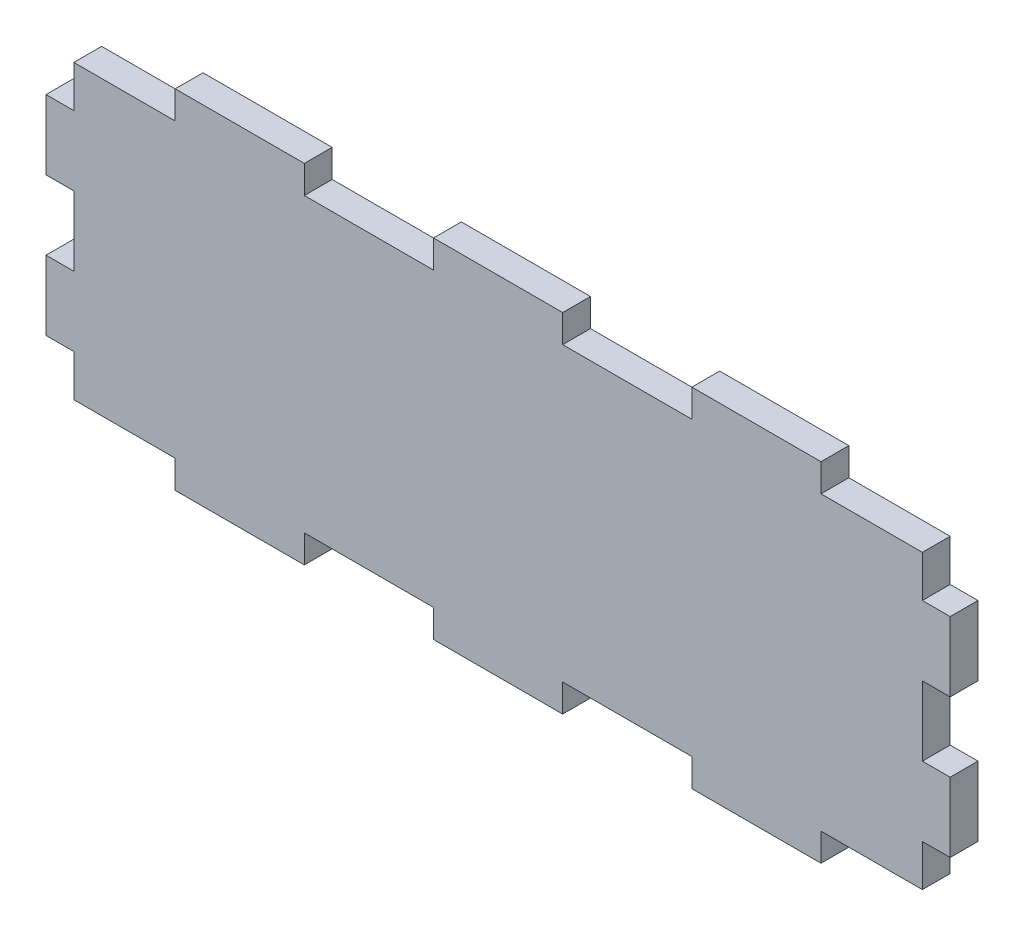
SolidWorks part; units mm, degrees
ref_plane "Front Plane" through (0, 0, 0) normal (0, 0, 1) x (1, 0, 0)
ref_plane "Top Plane" through (0, 0, 0) normal (0, 1, 0) x (1, 0, 0)
ref_plane "Right Plane" through (0, 0, 0) normal (1, 0, 0) x (0, 0, -1)
sketch "Buitenafmeting Rechthoek" plane through (0, 0, 0) normal (0, 0, 1) x (1, 0, 0)
  line L1 (0, 0) -> (130, 0)
  line L2 (0, 0) -> (0, 50)
  line L3 (0, 50) -> (130, 50)
  line L4 (130, 0) -> (130, 50)
  dimension "D1" = 130
  dimension "D2" = 50
extrude "Plaat" add sketch "Buitenafmeting Rechthoek" against normal blind 4
sketch "Tand Hor" plane through (0, 0, 0) normal (0, 0, 1) x (1, 0, 0)
  line L1 (130, 50) -> (0, 50) construction
  line L2 (0, 50) -> (18.5714, 50)
  line L3 (0, 50) -> (0, 46)
  line L4 (0, 46) -> (18.5714, 46)
  line L6 (18.5714, 50) -> (18.5714, 46)
  dimension "D1" = 4
  dimension "D2" = 18.5714
  dimension "D3" = 0
extrude "Tand Boven" cut sketch "Tand Hor" against normal through all
pattern_linear "Tanden Patroon Boven" count 4 spacing 37.1429 along (1, 0, 0) of "Tand Boven"
sketch "Tand Ver" plane through (0, 0, 0) normal (0, 0, 1) x (1, 0, 0)
  line L0 (0, 46) -> (0, 0) construction
  line L1 (0, 50) -> (4, 50)
  line L2 (0, 50) -> (0, 40)
  line L3 (0, 40) -> (4, 40)
  line L4 (4, 50) -> (4, 40)
  dimension "D1" = 4
  dimension "D2" = 10
  dimension "D3" = 50
extrude "Tand Links" cut sketch "Tand Ver" against normal through all
pattern_linear "Tanden Patroon Links" count 3 spacing 20 along (0, -1, 0) of "Tand Links"
sketch "Tand O" plane through (0, 0, 0) normal (0, 0, 1) x (1, 0, 0)
  line L0 (4, 0) -> (130, 0) construction
  line L1 (0, 0) -> (18.5714, 0)
  line L2 (0, 0) -> (0, 4)
  line L3 (0, 4) -> (18.5714, 4)
  line L4 (18.5714, 0) -> (18.5714, 4)
  dimension "D1" = 4
  dimension "D2" = 18.5714
  dimension "D3" = 0
extrude "Tand Onder" cut sketch "Tand O" against normal through all
pattern_linear "Tanden Patroon Onder" count 4 spacing 37.1429 along (1, 0, 0) of "Tand Onder"
sketch "Tand R" plane through (0, 0, 0) normal (0, 0, 1) x (1, 0, 0)
  line L0 (130, 4) -> (130, 46) construction
  line L1 (130, 50) -> (126, 50)
  line L2 (130, 50) -> (130, 40)
  line L3 (130, 40) -> (126, 40)
  line L4 (126, 50) -> (126, 40)
  dimension "D1" = 4
  dimension "D2" = 10
  dimension "D3" = 50
extrude "Tand Rechts" cut sketch "Tand R" against normal through all
pattern_linear "Tanden Patroon Rechts" count 3 spacing 20 along (0, -1, 0) of "Tand Rechts"
equation "\"D1@Buitenafmeting Rechthoek\"= \"Lengte\""
equation "\"D2@Buitenafmeting Rechthoek\" = \"Hoogte\""
equation "\"D1@Plaat\" = \"Dikte\""
equation "\"D3@Tanden Patroon Boven\" = \"LengteHorTand\" * 2"
equation "\"D1@Tanden Patroon Boven\" = \"nPatroonHor\""
equation "\"LengteHorTand\"= \"Lengte\" / \"nHor\"'Spatie tussen verschillende tanden in de lengte"
equation "\"nPatroonHor\"= ( \"nHor\" + 1 ) / 2 - \"GrensHor\"'Aantal kopies van tanden in de lengte"
equation "\"D1@Tand Hor\" = \"Dikte\""
equation "\"D2@Tand Hor\" = \"LengteHorTand\""
equation "\"D1@Tand Ver\" = \"Dikte\""
equation "\"LengteVertTand\"= \"Hoogte\" / \"nVert\"'Spatie tussen verschillende tanden in de hoogte"
equation "\"nPatroonVert\"= ( \"nVert\" + 1 ) / 2 - \"GrensVert\"'Aantal kopies van tanden in de hoogte"
equation "\"D2@Tand Ver\"=\"LengteVertTand\""
equation "\"D3@Tanden Patroon Links\"=\"LengteVertTand\"*2"
equation "\"D3@Tanden Patroon Rechts\"=\"LengteVertTand\"*2"
equation "\"D1@Tanden Patroon Rechts\"=\"nPatroonVert\""
equation "\"D3@Tanden Patroon Onder\"=\"LengteHorTand\"*2"
equation "\"D1@Tanden Patroon Onder\"=\"nPatroonHor\""
equation "\"D1@Tanden Patroon Links\"=\"nPatroonVert\""
equation "\"D3@Tand Ver\"=\"Hoogte\"-\"GrensVert\"*\"LengteVertTand\""
equation "\"D2@Tand R\" = \"LengteVertTand\""
equation "\"D3@Tand R\" = \"Hoogte\" - \"GrensVert\" * \"LengteVertTand\""
equation "\"D2@Tand O\"=\"LengteHorTand\""
equation "\"D3@Tand Hor\"=\"GrensHor\"*\"LengteHorTand\""
equation "\"D3@Tand O\"=\"GrensHor\"*\"LengteHorTand\""
equation "\"Tand Boven\"= IIF ( \"plaatsTandenBoven\" , \"unsuppressed\" , \"suppressed\" )"
equation "\"Tanden Patroon Boven\"= IIF ( \"plaatsTandenBoven\" , \"unsuppressed\" , \"suppressed\" )"
equation "\"Tand Links\"= IIF ( \"plaatsTandenLinks\" , \"unsuppressed\" , \"suppressed\" )"
equation "\"Tanden Patroon Links\"= IIF ( \"plaatsTandenLinks\" , \"unsuppressed\" , \"suppressed\" )"
equation "\"Tand Onder\"= IIF ( \"plaatsTandenOnder\" , \"unsuppressed\" , \"suppressed\" )"
equation "\"Tanden Patroon Onder\"= IIF ( \"plaatsTandenOnder\" , \"unsuppressed\" , \"suppressed\" )"
equation "\"Tand Rechts\"= IIF ( \"plaatsTandenRechts\" , \"unsuppressed\" , \"suppressed\" )"
equation "\"Tanden Patroon Rechts\"= IIF ( \"plaatsTandenRechts\" , \"unsuppressed\" , \"suppressed\" )"
equation "\"D1@Tand O\"=\"Dikte\""
equation "\"D1@Tand R\"=\"Dikte\""
